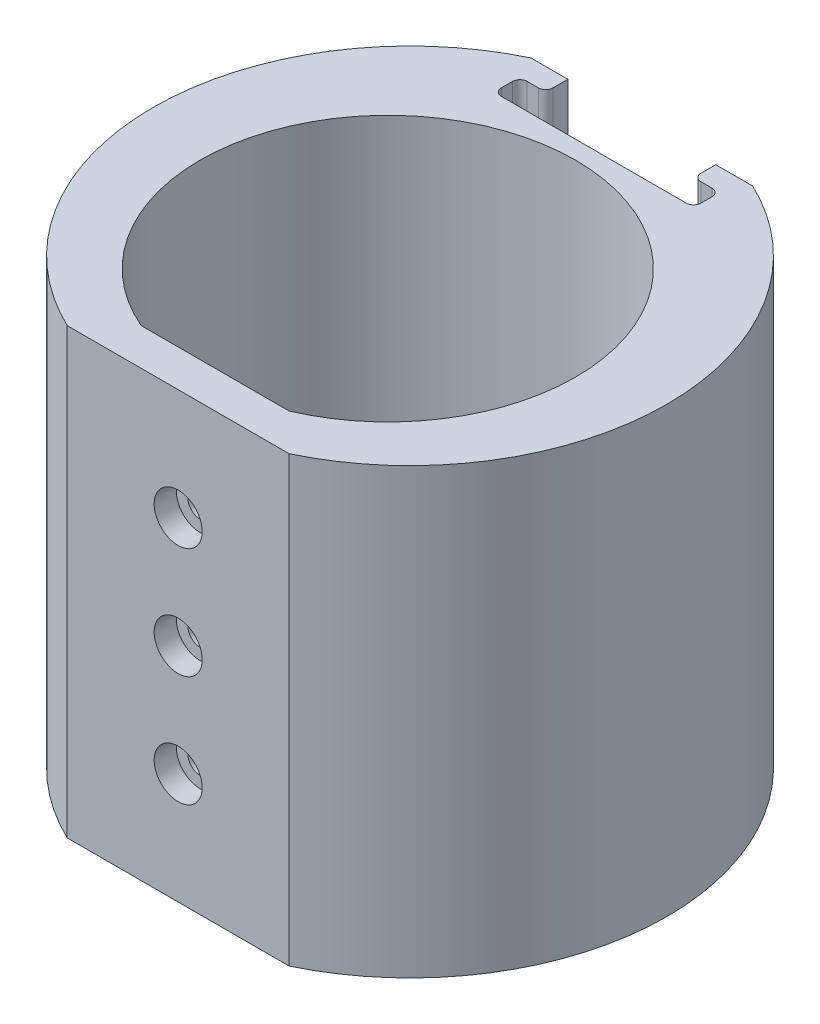
SolidWorks part; units mm, degrees
ref_plane "Front Plane" through (0, 0, 0) normal (0, 0, 1) x (1, 0, 0)
ref_plane "Top Plane" through (0, 0, 0) normal (0, 1, 0) x (1, 0, 0)
ref_plane "Right Plane" through (0, 0, 0) normal (1, 0, 0) x (0, 0, -1)
sketch "Sketch1" plane through (0, 0, 0) normal (0, 1, 0) x (1, 0, 0)
  line L0 (-10, -23.3487) -> (10, -23.3487)
  line L1 (-15, -28.3487) -> (15, -28.3487)
  line L2 (-15, 34.3487) -> (15, 34.3487)
  arc A0 (10, -23.3487) -> (-10, -23.3487) centre (0, 0) ccw
  arc A1 (15, -28.3487) -> (15, 34.3487) centre (0, 3) ccw
  arc A2 (-15, 34.3487) -> (-15, -28.3487) centre (0, 3) ccw
  point P5 (0, -28.3487)
  dimension "D1" = 50.8
  dimension "D4" = 3
  dimension "D2" = 20
  dimension "D3" = 5
  dimension "D5" = 30
  dimension "D6" = 30
extrude "Boss-Extrude1" add sketch "Sketch1" along normal mid plane 60
sketch "Sketch4" plane through (0, 30, 0) normal (0, 1, 0) x (1, 0, 0)
  line L0 (-10, 34.3487) -> (-10, 31.3487)
  line L2 (10, 31.3487) -> (10, 34.3487)
  line L3 (10, 34.3487) -> (-10, 34.3487)
  line L4 (-10, 31.3487) -> (-13.5, 31.3487)
  line L5 (-13.5, 31.3487) -> (-13.5, 27.8487)
  line L6 (-13.5, 27.8487) -> (13.5, 27.8487)
  line L7 (13.5, 27.8487) -> (13.5, 31.3487)
  line L8 (13.5, 31.3487) -> (10, 31.3487)
  line L9 (15, 34.3487) -> (-15, 34.3487) construction
  point P11 (0, 27.8487)
  point P12 (0, 34.3487)
  dimension "D1" = 3
  dimension "D2" = 27
  dimension "D3" = 3.5
  dimension "D4" = 20
extrude "Cut-Extrude1" cut sketch "Sketch4" against normal offset from surface (50 mm away) 10 up to face at (0, -30, -3)
fillet "Fillet1" radius 1 6 edges at (10, 5, -31.3487) (13.5, 5, -27.8487) (13.5, 5, -31.3487) (-13.5, 5, -27.8487) (-13.5, 5, -31.3487) (-10, 5, -31.3487)
hole_wizard "CBORE for M3 SHCS1" positions "Sketch5" profile "Sketch6" counterbore size "M3" standard "ANSI Metric"
sketch "Sketch5" plane through (0, 0, 28.3487) normal (0, 0, 1) x (1, 0, 0)
  line L0 (0, 0) -> (0, 15) construction
  line L1 (0, 0) -> (0, -15) construction
  point P0 (0, 0)
  point P15 (0, 15)
  point P16 (0, 0)
  point P17 (0, -15)
  dimension "D3" = 15
  dimension "D4" = 15
  dimension "D1" = 2
  dimension "D2" = 2
sketch "Sketch6" plane through (0, 0, 28.3487) normal (1, 0, 0) x (0, -1, 0)
  line L0 (0, 0) -> (0, 6.0215)
  line L1 (0, 6.0215) -> (1.7, 5)
  line L2 (1.7, 5) -> (1.7, 3)
  line L3 (1.7, 3) -> (3.25, 3)
  line L4 (3.25, 3) -> (3.25, 0)
  line L5 (3.25, 0) -> (0, 0)
  line L10 (0, 6.0215) -> (-1.7, 5) construction
  line L11 (0, -6.35) -> (0, 107.95) construction
  dimension "Hole Dia." = 3.4
  dimension "Hole Depth" = 5
  dimension "C'Bore Dia." = 6.5
  dimension "C'Bore Depth" = 3
  dimension "Drill Angle" = 118
